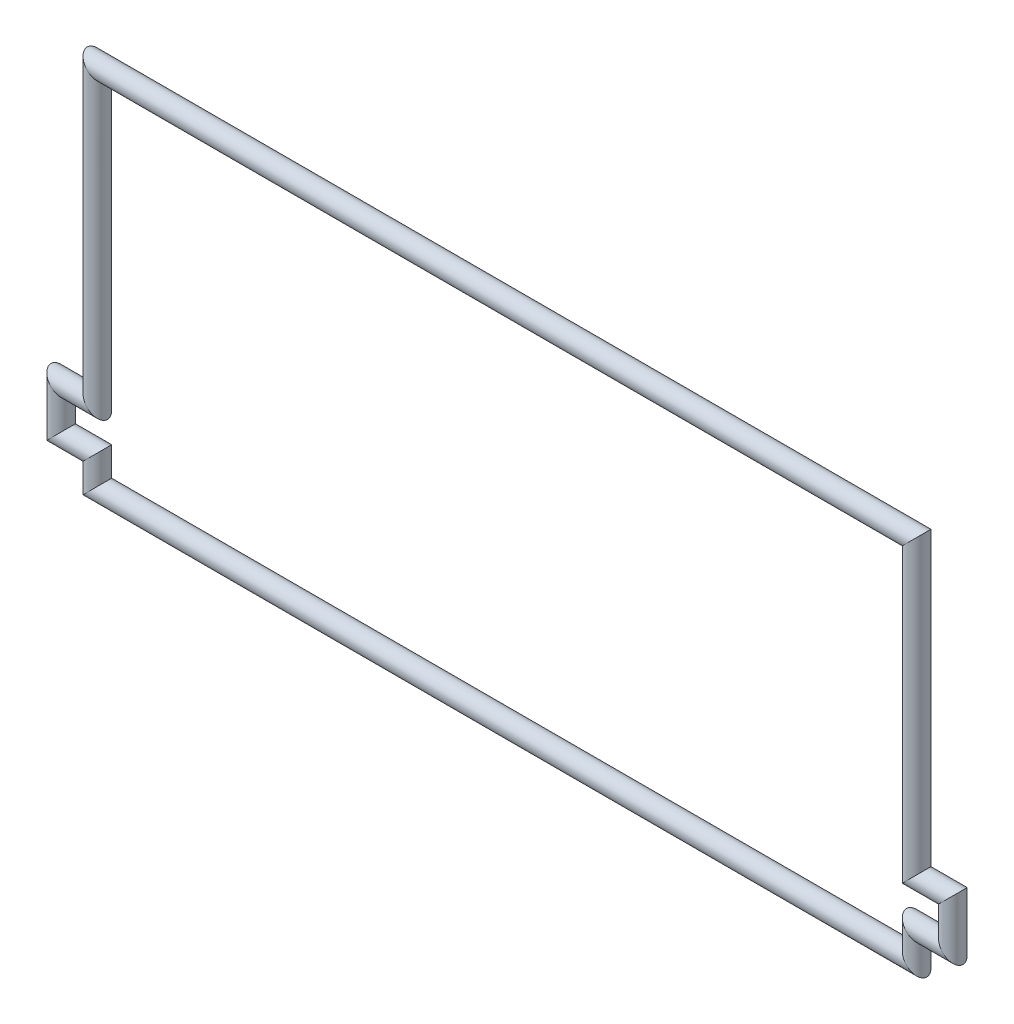
SolidWorks part; units mm, degrees
material "EPDM 60 Durometer"
ref_plane "Front Plane" through (0, 0, 0) normal (0, 0, 1) x (1, 0, 0)
ref_plane "Top Plane" through (0, 0, 0) normal (0, 1, 0) x (1, 0, 0)
ref_plane "Right Plane" through (0, 0, 0) normal (1, 0, 0) x (0, 0, -1)
sketch "Sketch1" plane through (0, 0, 0) normal (0, 0, 1) x (1, 0, 0)
  line L0 (0, 25.2) -> (56.5, 25.2)
  line L1 (56.5, 25.2) -> (56.5, 5.05)
  line L2 (56.5, 5.05) -> (59, 5.05)
  line L3 (59, 5.05) -> (59, 2)
  line L4 (59, 2) -> (56.5, 2)
  line L5 (56.5, 2) -> (56.5, 0)
  line L6 (56.5, 0) -> (0, 0)
  line L7 (0, 0) -> (0, 2)
  line L8 (0, 2) -> (-2.5, 2)
  line L9 (-2.5, 2) -> (-2.5, 5.05)
  line L10 (-2.5, 5.05) -> (0, 5.05)
  line L11 (0, 5.05) -> (0, 25.2)
  dimension "D1" = 56.5
  dimension "D2" = 25.2
  dimension "D3" = 3.05
  dimension "D4" = 2.5
  dimension "D5" = 2
sketch "Sketch2" plane through (0, 0, 0) normal (1, 0, 0) x (0, 0, -1)
  circle A0 centre (0, 0) radius 0.7
  dimension "D1" = 1.4
sweep "Sweep1" add profiles "Sketch2" path "Sketch1"
